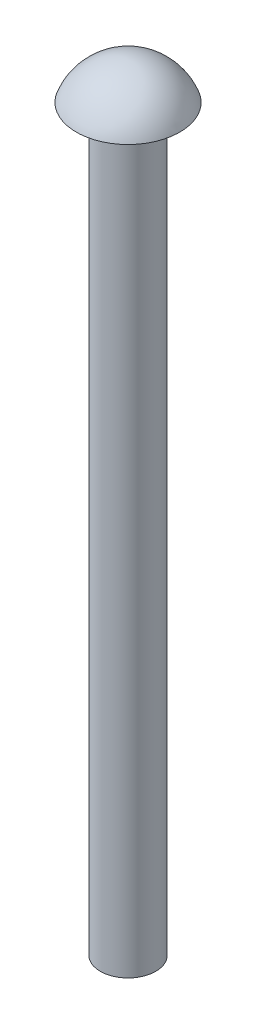
SolidWorks part; units mm, degrees
ref_plane "前视基准面" through (0, 0, 0) normal (0, 0, 1) x (1, 0, 0)
ref_plane "上视基准面" through (0, 0, 0) normal (0, 1, 0) x (1, 0, 0)
ref_plane "右视基准面" through (0, 0, 0) normal (1, 0, 0) x (0, 0, -1)
sketch "草图1" plane through (0, 0, 0) normal (0, 0, 1) x (1, 0, 0)
  line L0 (0, 0) -> (1.3, 0)
  line L1 (1.3, 0) -> (1.3, -40)
  line L2 (1.3, -40) -> (2.8, -40)
  line L3 (2.8, -40) -> (2.8, 2)
  arc A1 (2.8, 2) -> (0, 0) centre (2.8525, -1.0335) ccw
  dimension "D1" = 1.3
  dimension "D2" = 1.5
  dimension "D3" = 40
  dimension "D4" = 42
revolve "旋转1" add sketch "草图1" angle 360 about L3
